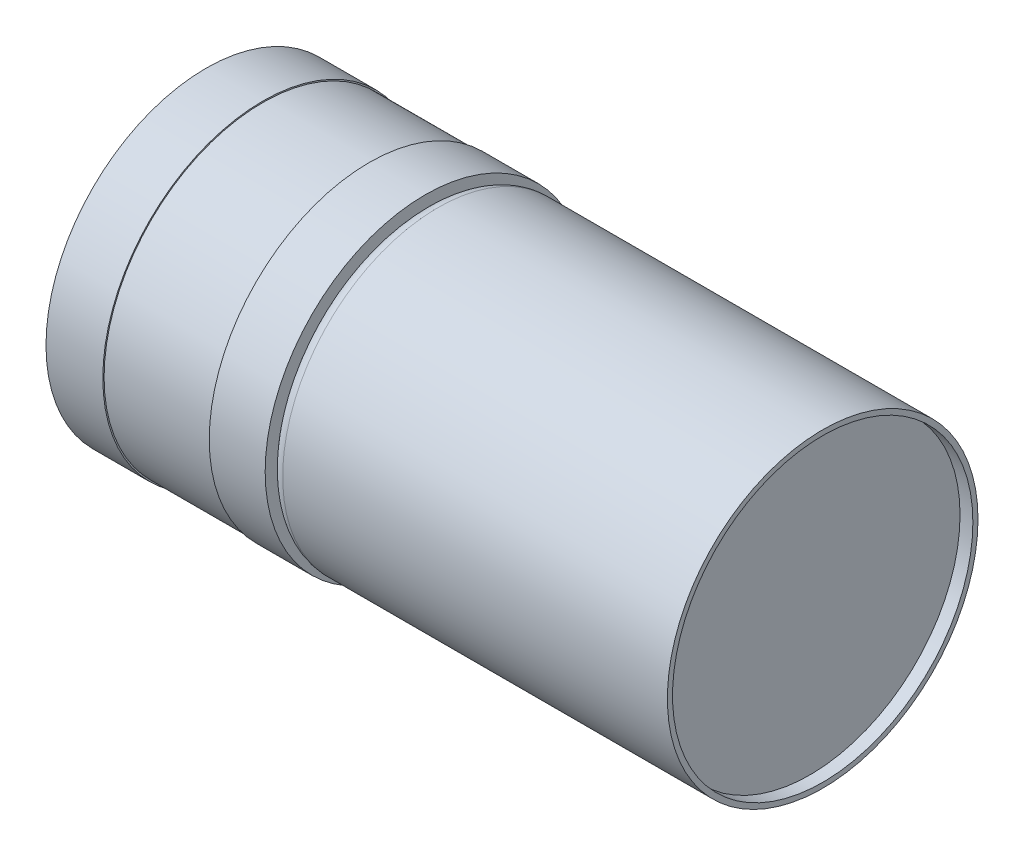
SolidWorks part; units mm, degrees
ref_plane "Front Plane" through (0, 0, 0) normal (0, 0, 1) x (1, 0, 0)
ref_plane "Top Plane" through (0, 0, 0) normal (0, 1, 0) x (1, 0, 0)
ref_plane "Right Plane" through (0, 0, 0) normal (1, 0, 0) x (0, 0, -1)
sketch "Sketch1" plane through (0, 0, 0) normal (1, 0, 0) x (0, 0, -1)
  circle A0 centre (0, 0) radius 12.11
  dimension "D1" = 24.22
extrude "Boss-Extrude1" add sketch "Sketch1" along normal blind 31
fillet "Fillet1" radius 1 1 edges at (0, 0, -12.11)
sketch "Sketch2" plane through (31, 0, 0) normal (1, 0, 0) x (0, 0, -1)
  circle A0 centre (0, 0) radius 11.71
  circle A1 centre (0, 0) radius 12.11 construction
  dimension "D1" = 0.4
extrude "Cut-Extrude1" cut sketch "Sketch2" against normal blind 1
sketch "Sketch3" plane through (0, 0, 0) normal (-1, 0, 0) x (0, 0, 1)
  circle A0 centre (0, 0) radius 12.475
  dimension "D1" = 24.95
extrude "Boss-Extrude2" add sketch "Sketch3" along normal blind 4.36
sketch "Sketch4" plane through (-4.36, 0, 0) normal (-1, 0, 0) x (0, 0, 1)
  circle A0 centre (0, 0) radius 12.375
  dimension "D1" = 24.75
extrude "Boss-Extrude3" add sketch "Sketch4" along normal blind 8.3
sketch "Sketch5" plane through (-12.66, 0, 0) normal (-1, 0, 0) x (0, 0, 1)
  circle A0 centre (0, 0) radius 12.475
  dimension "D1" = 24.95
extrude "Boss-Extrude4" add sketch "Sketch5" along normal blind 4.43
sketch "Sketch6" plane through (-17.09, 0, 0) normal (-1, 0, 0) x (0, 0, 1)
  line L0 (0, 12.475) -> (0, -12.475) construction
  line L1 (-12.475, 0) -> (12.475, 0) construction
  circle A0 centre (0, 0) radius 12.475 construction
  circle A1 centre (0, 8.5) radius 1.4
  circle A2 centre (0, -8.5) radius 1.4
  dimension "D2" = 2.8
  dimension "D1" = 17
extrude "Cut-Extrude2" cut sketch "Sketch6" against normal blind 6
